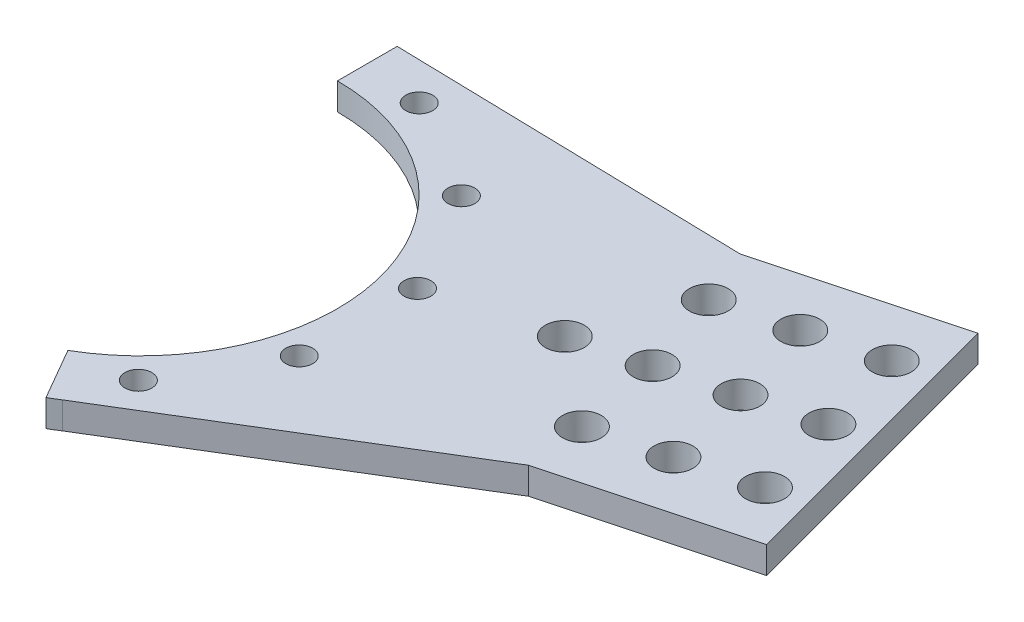
SolidWorks part; units mm, degrees
ref_plane "Front Plane" through (0, 0, 0) normal (0, 0, 1) x (1, 0, 0)
ref_plane "Top Plane" through (0, 0, 0) normal (0, 1, 0) x (1, 0, 0)
ref_plane "Right Plane" through (0, 0, 0) normal (1, 0, 0) x (0, 0, -1)
sketch "Sketch1" plane through (0, 0, 0) normal (0, 1, 0) x (1, 0, 0)
  line L0 (0, 33) -> (0, 43)
  line L1 (16.5, -28.5788) -> (21.5, -37.2391)
  arc A0 (0, 43) -> (21.5, -37.2391) centre (0, 0) cw
  arc A1 (0, 33) -> (16.5, -28.5788) centre (0, 0) cw
  dimension "D1" = 150
  dimension "D2" = 33
  dimension "D3" = 43
extrude "Boss-Extrude1" add sketch "Sketch1" along normal mid plane 4.5
sketch "Sketch4" plane through (0, 0, 0) normal (0, 1, 0) x (1, 0, 0)
  line L0 (0, 0) -> (64.2341, 17.2115) construction
  line L1 (90.1221, 50.0301) -> (25.4051, 32.6892)
  line L2 (90.1221, 50.0301) -> (103.0631, 1.7338)
  line L3 (25.4051, 32.6892) -> (38.346, -15.6071)
  line L4 (103.0631, 1.7338) -> (38.346, -15.6071)
  line L5 (31.8756, 8.541) -> (96.5926, 25.8819) construction
  line L6 (57.7636, 41.3596) -> (70.7045, -6.9367) construction
  line L7 (0, 43) -> (0, 33) construction
  arc A1 (16.5, -28.5788) -> (0, 33) centre (0, 0) ccw construction
  dimension "D1" = 75
  dimension "D2" = 100
  dimension "D3" = 50
extrude "Boss-Extrude2" add sketch "Sketch4" along normal mid plane 4.5
sketch "Sketch5" plane through (0, 0, 0) normal (0, 1, 0) x (1, 0, 0)
  line L0 (0, 0) -> (96.5926, 25.8819) construction
  line L1 (103.0631, 1.7338) -> (90.1221, 50.0301) construction
  line L2 (0, 43) -> (58.7226, 41.6166)
  line L3 (90.1221, 50.0301) -> (27.3231, 33.2031) construction
  line L4 (58.7226, 41.6166) -> (27.3231, 33.2031)
  line L5 (27.3231, 33.2031) -> (0, 43)
  line L6 (71.6636, -6.6797) -> (40.2641, -15.0932)
  line L7 (21.5, -37.2391) -> (71.6636, -6.6797)
  line L8 (40.2641, -15.0932) -> (21.5, -37.2391)
extrude "Boss-Extrude3" add sketch "Sketch5" along normal mid plane 4.5
sketch "Sketch2" plane through (0, 2.25, 0) normal (0, 1, 0) x (1, 0, 0)
  arc A0 (18.6469, -33.1103) -> (0, 38) centre (0, 0) ccw construction
  circle A1 centre (36.7573, 9.6387) radius 2.25
  dimension "D1" = 4.5
  dimension "D2" = 38
extrude "Cut-Extrude1" cut sketch "Sketch2" against normal through all both and the other way through all
pattern_circular "CirPattern1" count 3 every 30 about axis through (0, 0, 0) along (0, 1, 0) of "Cut-Extrude1"
sketch "Sketch6" plane through (0, 2.25, 0) normal (0, 1, 0) x (1, 0, 0)
  line L0 (0, 0) -> (96.5926, 25.8819) construction
  line L1 (103.0631, 1.7338) -> (90.1221, 50.0301) construction
  line L2 (86.9147, 38.8179) -> (94.6793, 9.8401) construction
  circle A0 centre (94.6793, 9.8401) radius 3.25
  circle A1 centre (86.9147, 38.8179) radius 3.25
  point P8 (90.797, 24.329)
  dimension "D1" = 6.5
  dimension "D2" = 30
  dimension "D3" = 6
extrude "Cut-Extrude2" cut sketch "Sketch6" against normal through all both and the other way through all
pattern_linear "LPattern1" count 3 spacing 12.5 along (-0.9659, 0, 0.2588) of "Cut-Extrude2"
sketch "Sketch7" plane through (0, 2.25, 0) normal (0, 1, 0) x (1, 0, 0)
  line L0 (0, 0) -> (96.5926, 25.8819) construction
  line L1 (103.0631, 1.7338) -> (90.1221, 50.0301) construction
  circle A0 centre (90.797, 24.329) radius 3.25
  dimension "D1" = 6.5
  dimension "D2" = 6
extrude "Cut-Extrude3" cut sketch "Sketch7" against normal blind 10
pattern_linear "LPattern2" count 4 spacing 12 along (-0.9659, 0, 0.2588) of "Cut-Extrude3"
sketch "Sketch8" plane through (0, 0, 0) normal (0, 1, 0) x (1, 0, 0)
  line L0 (0, 33) -> (0, 0)
  line L1 (0, 33) -> (5, 33)
  line L2 (0, 0) -> (5, 0)
  line L3 (5, 33) -> (5, 0)
  line L4 (16.5, -28.5788) -> (0, 0)
  line L5 (16.5, -28.5788) -> (20.8301, -26.0788)
  line L6 (0, 0) -> (4.3301, 2.5)
  line L7 (20.8301, -26.0788) -> (4.3301, 2.5)
  line L8 (0, 0) -> (36.7573, 9.6387) construction
  line L9 (32.91, 11.2143) -> (-0.6341, 2.4182)
  line L10 (32.91, 11.2143) -> (34.1782, 6.3778)
  line L11 (-0.6341, 2.4182) -> (0.6341, -2.4182)
  line L12 (34.1782, 6.3778) -> (0.6341, -2.4182)
  line L13 (0, 0) -> (33.5441, 8.7961) construction
  line L14 (16.1379, 6.8163) -> (17.4062, 1.9798) construction
  circle A0 centre (0, 0) radius 9
  circle A1 centre (0, 0) radius 15
  point P15 (16.772, 4.398)
  dimension "D1" = 18
  dimension "D2" = 30
  dimension "D3" = 5
extrude "Boss-Extrude4" [suppressed] add sketch "Sketch8" along normal mid plane 4.5 contours L0 A1 L4 A0 | L9 A1 L3 A0 | L7 A1 L12 A0 | A1 L4 L5 L7 | L4 A1 L7 A0 | A1 L3 L1 L0 | L3 A1 L0 A0 | L12 A1 L9 A0 | A1 L12 L10 L9
